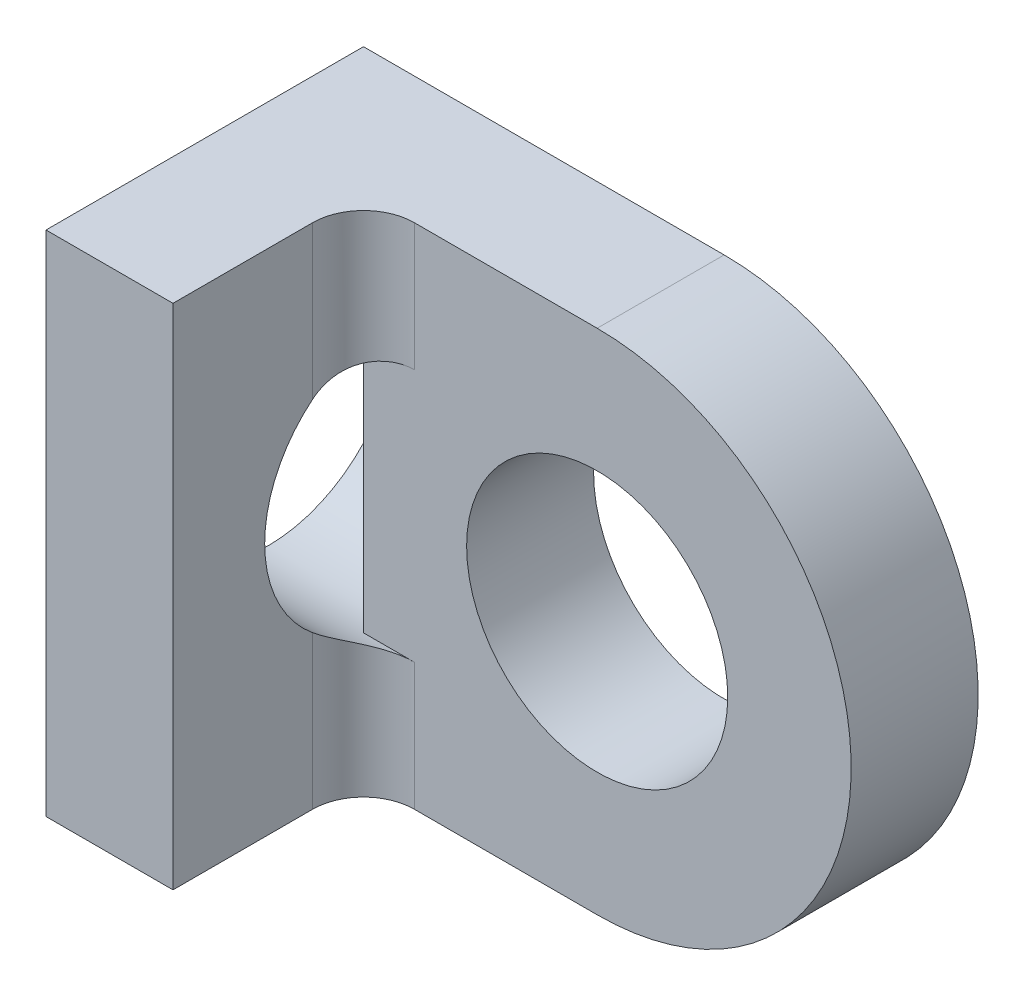
SolidWorks part; units mm, degrees
material "ABS"
ref_plane "Front Plane" through (0, 0, 0) normal (0, 0, 1) x (1, 0, 0)
ref_plane "Top Plane" through (0, 0, 0) normal (0, 1, 0) x (1, 0, 0)
ref_plane "Right Plane" through (0, 0, 0) normal (1, 0, 0) x (0, 0, -1)
sketch "Sketch1" plane through (0, 0, 0) normal (0, 0, 1) x (1, 0, 0)
  line L0 (0, 0) -> (-9.017, 0) construction
  line L1 (-9.017, -6.35) -> (-9.017, 6.35)
  line L2 (-9.017, 6.35) -> (0, 6.35)
  line L3 (0, 6.35) -> (0, 0) construction
  line L4 (-9.017, -6.35) -> (0, -6.35)
  circle A0 centre (0, 0) radius 3.2639
  arc A1 (0, 6.35) -> (0, -6.35) centre (0, 0) cw
  dimension "D1" = 6.5278
  dimension "D2" = 9.017
  dimension "D3" = 6.35
extrude "Boss-Extrude1" add sketch "Sketch1" along normal blind 3.175 contours A1 L2 L1 L4 A0
sketch "Sketch2" plane through (0, 0, 3.175) normal (0, 0, 1) x (1, 0, 0)
  line L0 (-9.017, -6.35) -> (-9.017, 6.35) construction
  line L1 (-9.017, 6.35) -> (-5.842, 6.35)
  line L2 (-9.017, 6.35) -> (-9.017, -6.35)
  line L3 (-9.017, -6.35) -> (-5.842, -6.35)
  line L4 (-5.842, 6.35) -> (-5.842, -6.35)
  line L5 (-9.017, -6.35) -> (0, -6.35) construction
  line L6 (-9.017, 6.35) -> (0, 6.35) construction
  dimension "D1" = 3.175
extrude "Boss-Extrude2" add sketch "Sketch2" along normal blind 4.7625
sketch "Sketch3" plane through (-9.017, 0, 0) normal (-1, 0, 0) x (0, 0, 1)
  line L0 (0, 0) -> (2.3812, 0) construction
  line L1 (0, -6.35) -> (0, 6.35) construction
  circle A0 centre (2.3812, 0) radius 3.2639
  dimension "D2" = 6.5278
  dimension "D1" = 2.3812
extrude "Cut-Extrude1" cut sketch "Sketch3" against normal blind 3.175
fillet "Fillet2" radius 1.27 2 edges at (-5.842, -4.758, 3.175) (-5.842, 4.758, 3.175)
